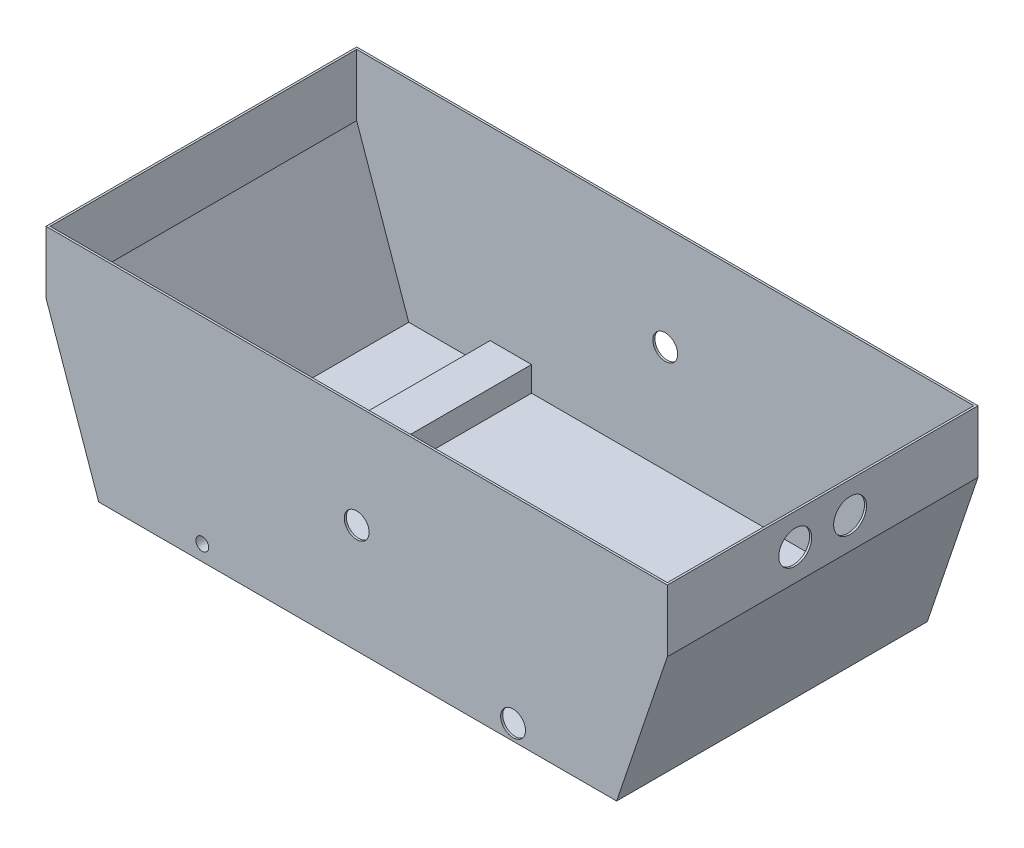
SolidWorks part; units mm, degrees
ref_plane "Front Plane" through (0, 0, 0) normal (0, 0, 1) x (1, 0, 0)
ref_plane "Top Plane" through (0, 0, 0) normal (0, 1, 0) x (1, 0, 0)
ref_plane "Right Plane" through (0, 0, 0) normal (1, 0, 0) x (0, 0, -1)
sketch "Sketch1" plane through (0, 0, 0) normal (0, 0, 1) x (1, 0, 0)
  line L0 (-49.7914, 32.6453) -> (-19.7914, 32.6453)
  line L1 (-19.7914, 32.6453) -> (-19.7914, 29.6453)
  line L2 (-49.7914, 32.6453) -> (-49.7914, 29.6453)
  line L6 (-47.2477, 22.3886) -> (-22.239, 22.3886)
  line L8 (-49.7914, 29.6453) -> (-47.2477, 22.3886)
  line L9 (-19.7914, 29.6453) -> (-22.239, 22.3886)
extrude "Boss-Extrude1" add sketch "Sketch1" along normal blind 15
sketch "Sketch2" plane through (0, 32.6453, 0) normal (0, 1, 0) x (1, 0, 0)
sketch "Sketch3" plane through (0, 32.6453, 0) normal (0, 1, 0) x (1, 0, 0)
  line L1 (-49.7914, 0) -> (-19.7914, 0)
  line L2 (-49.7914, 0) -> (-49.7914, -15)
  line L3 (-49.7914, -15) -> (-19.7914, -15)
  line L4 (-19.7914, 0) -> (-19.7914, -15)
sketch "Sketch4" plane through (0, 32.6453, 0) normal (0, 1, 0) x (1, 0, 0)
  line L1 (-48.7975, -0.248) -> (-20.6113, -0.248)
  line L2 (-48.7975, -0.248) -> (-48.7975, -14.7555)
  line L3 (-48.7975, -14.7555) -> (-20.6113, -14.7555)
  line L4 (-20.6113, -0.248) -> (-20.6113, -14.7555)
sketch "Sketch5" plane through (0, 0, 15) normal (0, 0, 1) x (1, 0, 0)
  circle A0 centre (-43.9573, 24.0758) radius 0.129
scale "Scale4" bodies to scale 103 scale about centroid uniform scaling yes scale factor 10
sketch "Sketch6" plane through (0, 0, 82.5) normal (0, 0, 1) x (1, 0, 0)
  line L0 (-162.128, -17.7919) -> (93.1178, -17.7919)
  line L1 (-184.9359, 47.2758) -> (-159.4991, -25.2919) construction
  line L2 (90.5882, -25.2919) -> (115.0641, 47.2758) construction
  line L3 (-159.4991, -25.2919) -> (90.5882, -25.2919) construction
  circle A0 centre (-109.4991, -17.7919) radius 2.5
  circle A1 centre (-109.4991, -17.7919) radius 3.1
  circle A2 centre (-109.4991, -17.7919) radius 2.95
  dimension "D2" = 5
  dimension "D4" = 6.2
  dimension "D1" = 7.5
  dimension "D3" = 50
sketch "Sketch7" plane through (0, 0, 82.5) normal (0, 0, 1) x (1, 0, 0)
  line L1 (-159.4991, -25.2919) -> (90.5882, -25.2919) construction
  circle A0 centre (40.5882, -17.7919) radius 2.5
  dimension "D1" = 7.5
  dimension "D2" = 50
sketch "Sketch8" plane through (0, 0, 82.5) normal (0, 0, 1) x (1, 0, 0)
  line L0 (115.0641, 77.2758) -> (-184.9359, 77.2758) construction
  circle A0 centre (-34.9359, 27.2758) radius 2.5
  dimension "D1" = 50
  dimension "D2" = 150
shell "Shell3" thickness 1
extrude "Cut-Extrude2" cut sketch "Sketch7" against normal through all both and the other way through all contours A0
extrude "Cut-Extrude3" cut sketch "Sketch8" against normal through all both and the other way through all contours A0
sketch "Sketch11" plane through (0, 0, -67.5) normal (0, 0, -1) x (-1, 0, 0)
  circle A0 centre (-40.5882, -17.7919) radius 6
extrude "Cut-Extrude5" cut sketch "Sketch11" against normal through all both and the other way through all
sketch "Sketch12" plane through (0, 0, 82.5) normal (0, 0, 1) x (1, 0, 0)
  circle A0 centre (-34.9359, 27.2758) radius 6
extrude "Cut-Extrude6" cut sketch "Sketch12" against normal through all both and the other way through all
sketch "Sketch13" plane through (115.0641, 0, 0) normal (1, 0, 0) x (0, 0, -1)
  text T0 "resq"
sketch "Sketch19" plane through (0, -24.2919, 0) normal (0, 1, 0) x (1, 0, 0)
  line L0 (-119.4991, 66.5) -> (-119.4991, -81.5)
  line L1 (-158.7899, 66.5) -> (89.8701, 66.5) construction
  line L2 (-158.7899, -81.5) -> (89.8701, -81.5) construction
  line L3 (-119.4991, -81.5) -> (-99.4991, -81.5)
  line L4 (-99.4991, -81.5) -> (-99.4991, 66.5)
  line L5 (-99.4991, 66.5) -> (-119.4991, 66.5)
  point P6 (-109.4991, -81.5)
  dimension "D1" = 20
extrude "Boss-Extrude6" add sketch "Sketch19" along normal blind 12
extrude "Cut-Extrude9" cut sketch "Sketch6" against normal through all both and the other way through all contours A1
sketch "Sketch21" plane through (0, 0, 82.5) normal (0, 0, 1) x (1, 0, 0)
  circle A0 centre (-109.4991, -17.7919) radius 3.1 construction
  point P0 (-109.4991, -20.8919)
sketch "Sketch22" plane through (115.0641, 0, 0) normal (1, 0, 0) x (0, 0, -1)
  line L0 (-7.5, 77.2758) -> (-7.5, 47.2758) construction
  line L1 (-82.5, 77.2758) -> (67.5, 77.2758) construction
  line L2 (-82.5, 47.2758) -> (67.5, 47.2758) construction
  circle A0 centre (-20.75, 62.2758) radius 7.95
  circle A1 centre (5.75, 62.2758) radius 7.95
  point P9 (-7.5, 62.2758)
  dimension "D1" = 26.5
extrude "Cut-Extrude10" cut sketch "Sketch22" against normal blind 2
